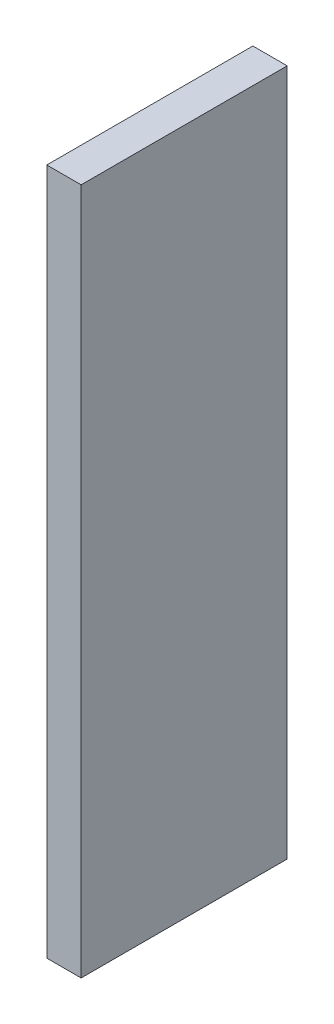
SolidWorks part; units mm, degrees
ref_plane "Plan de face" through (0, 0, 0) normal (0, 0, 1) x (1, 0, 0)
ref_plane "Plan de dessus" through (0, 0, 0) normal (0, 1, 0) x (1, 0, 0)
ref_plane "Plan de droite" through (0, 0, 0) normal (1, 0, 0) x (0, 0, -1)
sketch "Esquisse1" plane through (0, 0, 0) normal (0, 0, 1) x (1, 0, 0)
  line L1 (-33.3975, 953.2259) -> (16.6025, 953.2259)
  line L2 (-33.3975, 953.2259) -> (-33.3975, -46.7741)
  line L3 (-33.3975, -46.7741) -> (16.6025, -46.7741)
  line L4 (16.6025, 953.2259) -> (16.6025, -46.7741)
  dimension "D1" = 1000
  dimension "D2" = 50
extrude "Boss.-Extru.1" add sketch "Esquisse1" along normal blind 300
